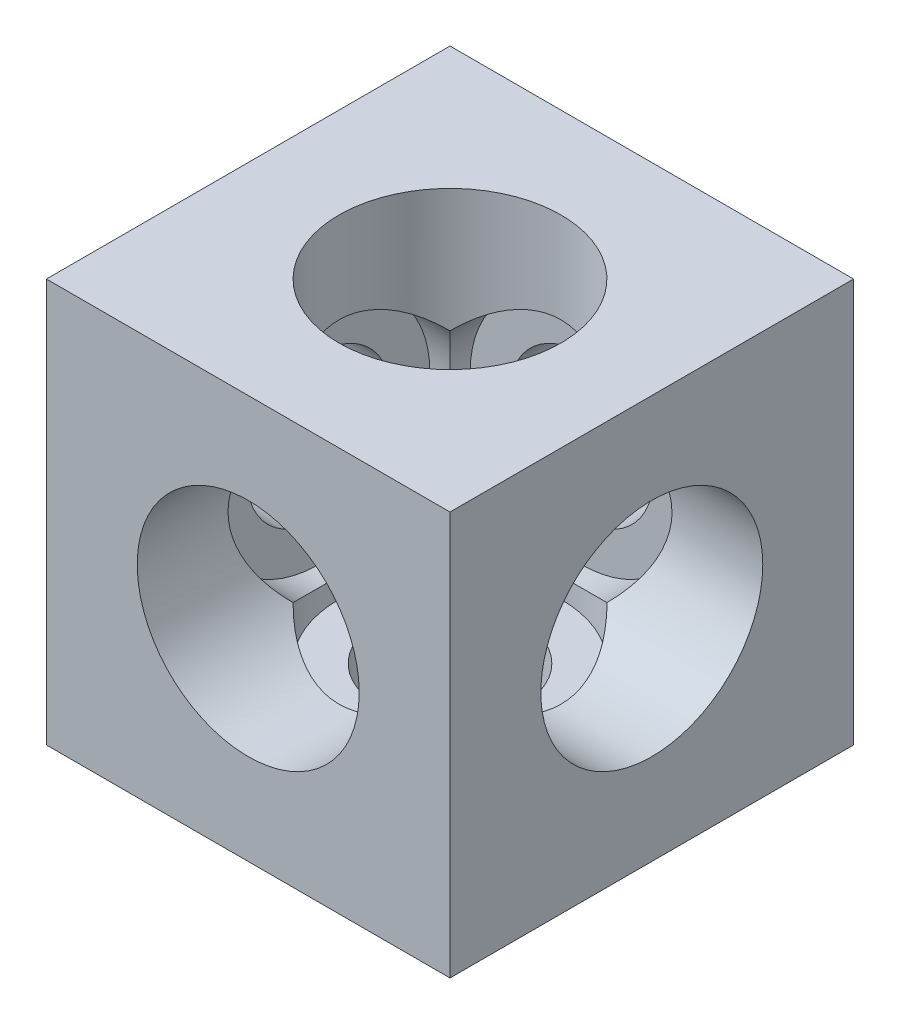
SolidWorks part; units mm, degrees
material "CA"
ref_plane "Plan de face" through (0, 0, 0) normal (0, 0, 1) x (1, 0, 0)
ref_plane "Plan de dessus" through (0, 0, 0) normal (0, 1, 0) x (1, 0, 0)
ref_plane "Plan de droite" through (0, 0, 0) normal (1, 0, 0) x (0, 0, -1)
sketch "Esquisse1" plane through (0, 0, 0) normal (0, 0, 1) x (1, 0, 0)
  line L1 (-10, -10) -> (10, -10)
  line L2 (-10, -10) -> (-10, 10)
  line L3 (-10, 10) -> (10, 10)
  line L4 (10, -10) -> (10, 10)
  line L5 (-10, -10) -> (10, 10) construction
  line L6 (-10, 10) -> (10, -10) construction
  point P0 (0, 0)
  dimension "D1" = 20
extrude "Boss.-Extru.1" add sketch "Esquisse1" along normal mid plane 20
sketch "Esquisse2" plane through (0, 0, 10) normal (0, 0, 1) x (1, 0, 0)
  circle A0 centre (0, 0) radius 3.57
  dimension "D1" = 7.14
extrude "Enlèv. mat.-Extru.1" cut sketch "Esquisse2" against normal through all
sketch "Esquisse3" plane through (0, 0, 10) normal (0, 0, 1) x (1, 0, 0)
  circle A0 centre (0, 0) radius 5.5
  dimension "D1" = 11
extrude "Enlèv. mat.-Extru.2" cut sketch "Esquisse3" against normal offset from surface (16.5 mm away) 3.5 up to face at (3.57, 0, -10)
sketch "Esquisse4" plane through (10, 0, 0) normal (1, 0, 0) x (0, 0, -1)
  circle A0 centre (0, 0) radius 3.57
  dimension "D1" = 7.14
extrude "Enlèv. mat.-Extru.3" cut sketch "Esquisse4" against normal through all
sketch "Esquisse5" plane through (10, 0, 0) normal (1, 0, 0) x (0, 0, -1)
  circle A0 centre (0, 0) radius 5.5
  dimension "D1" = 11
extrude "Enlèv. mat.-Extru.4" cut sketch "Esquisse5" against normal offset from surface (16.5 mm away) 3.5 up to face at (-10, 0, -3.57)
sketch "Esquisse6" plane through (0, 10, 0) normal (0, 1, 0) x (1, 0, 0)
  circle A0 centre (0, 0) radius 3.57
  dimension "D1" = 7.14
extrude "Enlèv. mat.-Extru.5" cut sketch "Esquisse6" against normal through all
sketch "Esquisse7" plane through (0, 10, 0) normal (0, 1, 0) x (1, 0, 0)
  circle A0 centre (0, 0) radius 5.5
  dimension "D1" = 11
extrude "Enlèv. mat.-Extru.6" cut sketch "Esquisse7" against normal offset from surface (16.5 mm away) 3.5 up to face at (0, -10, 3.57)
